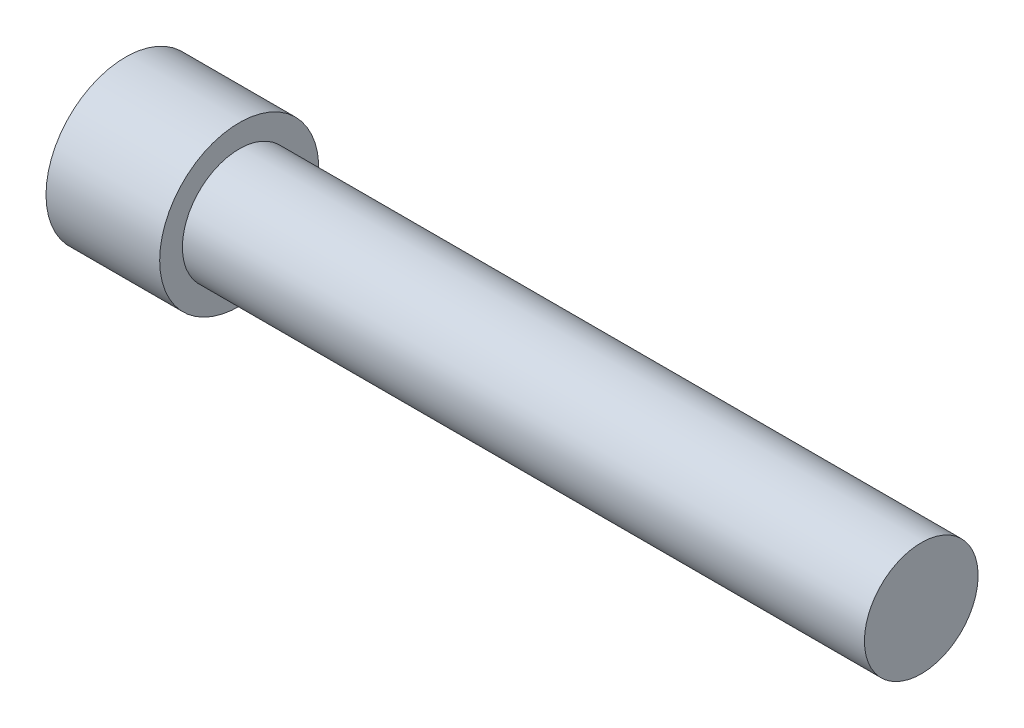
SolidWorks part; units mm, degrees
ref_plane "Front Plane" through (0, 0, 0) normal (0, 0, 1) x (1, 0, 0)
ref_plane "Top Plane" through (0, 0, 0) normal (0, 1, 0) x (1, 0, 0)
ref_plane "Right Plane" through (0, 0, 0) normal (1, 0, 0) x (0, 0, -1)
sketch "Sketch1" plane through (0, 0, 0) normal (0, 0, 1) x (1, 0, 0)
  line L0 (0, 0) -> (35, 0)
  line L1 (0, 0) -> (0, 3.5)
  line L2 (0, 3.5) -> (5, 3.5)
  line L3 (5, 3.5) -> (5, 2.5)
  line L4 (5, 2.5) -> (35, 2.5)
  line L5 (35, 2.5) -> (35, 0)
revolve "Revolve1" add sketch "Sketch1" angle 360 about L0
